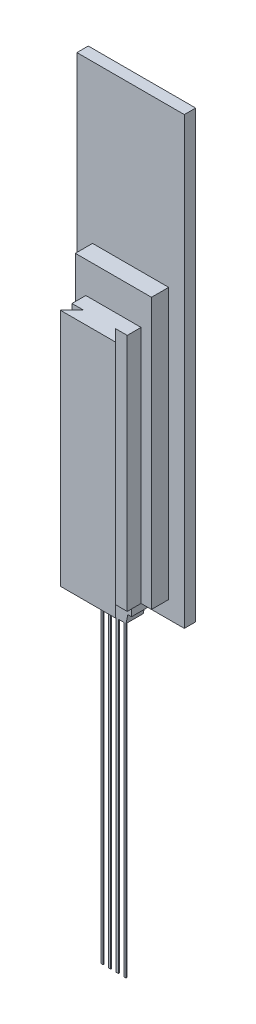
SolidWorks part; units mm, degrees
ref_plane "Front Plane" through (0, 0, 0) normal (0, 0, 1) x (1, 0, 0)
ref_plane "Top Plane" through (0, 0, 0) normal (0, 1, 0) x (1, 0, 0)
ref_plane "Right Plane" through (0, 0, 0) normal (1, 0, 0) x (0, 0, -1)
sketch "Sketch1" plane through (0, 0, 0) normal (0, 0, 1) x (1, 0, 0)
  line L1 (-1.75, 7.25) -> (1.75, 7.25)
  line L2 (-1.75, 7.25) -> (-1.75, -7.25)
  line L3 (-1.75, -7.25) -> (1.75, -7.25)
  line L4 (1.75, 7.25) -> (1.75, -7.25)
  line L5 (-1.75, 7.25) -> (1.75, -7.25) construction
  line L6 (-1.75, -7.25) -> (1.75, 7.25) construction
  point P0 (0, 0)
  dimension "D1" = 3.5
  dimension "D2" = 14.5
extrude "Boss-Extrude1" add sketch "Sketch1" along normal blind 0.37
sketch "Sketch2" plane through (0, 0, 0.37) normal (0, 0, 1) x (1, 0, 0)
  line L0 (-1.75, -7.25) -> (1.75, -7.25) construction
  line L1 (-1.24, 2.12) -> (1.24, 2.12)
  line L2 (-1.24, 2.12) -> (-1.24, -6.69)
  line L3 (-1.24, -6.69) -> (1.24, -6.69)
  line L4 (1.24, 2.12) -> (1.24, -6.69)
  line L5 (-1.24, 2.12) -> (1.24, -6.69) construction
  line L6 (-1.24, -6.69) -> (1.24, 2.12) construction
  line L7 (-0.47, -7.22) -> (-0.41, -7.5037)
  line L8 (0.59, -7.22) -> (-0.59, -7.22)
  line L9 (0.59, -7.22) -> (0.59, -6.69)
  line L10 (0.59, -6.69) -> (-0.59, -6.69)
  line L11 (-0.59, -7.22) -> (-0.59, -6.69)
  line L12 (0.59, -7.22) -> (-0.59, -6.69) construction
  line L13 (0.59, -6.69) -> (-0.59, -7.22) construction
  line L14 (-0.41, -7.5037) -> (0.41, -7.5037)
  line L15 (0.41, -7.5037) -> (0.47, -7.22)
  line L16 (0.47, -7.22) -> (-0.47, -7.22)
  point P0 (0, -2.285)
  point P8 (0, -6.955)
  line M8 (-1.75, -7.25) -> (1.75, -7.25)
  dimension "D1" = 0.56
  dimension "D2" = 2.48
  dimension "D3" = 8.81
  dimension "D4" = 0
  dimension "D5" = 0
  dimension "D6" = 0.53
  dimension "D7" = 1.18
  dimension "D8" = 0.12
  dimension "D9" = 0.12
  dimension "D10" = 0.29
  dimension "D11" = 0.82
  dimension "D12" = 0.29
extrude "Boss-Extrude2" add sketch "Sketch2" along normal blind 0.56 contours L4 L1 L2 L3 | L11 L8 L9 L3 | L14 L15 L7 M8 | L15 L8 L7 M8
sketch "Sketch3" plane through (0, 0, 0.93) normal (0, 0, 1) x (1, 0, 0)
  line L0 (-0.41, -7.5037) -> (-0.34, -7.5037)
  line L1 (-0.41, -7.5037) -> (-0.41, -17.5037)
  line L2 (-0.34, -7.5037) -> (-0.34, -17.5037)
  line L3 (-0.41, -17.5037) -> (-0.34, -17.5037)
  line L4 (-0.41, -7.5037) -> (0.41, -7.5037) construction
  line L5 (-0.16, -7.5037) -> (-0.09, -7.5037)
  line L6 (-0.16, -7.5037) -> (-0.16, -17.5037)
  line L7 (-0.09, -7.5037) -> (-0.09, -17.5037)
  line L8 (-0.16, -17.5037) -> (-0.09, -17.5037)
  line L9 (0.16, -7.5037) -> (0.09, -7.5037)
  line L10 (0.16, -7.5037) -> (0.16, -17.5037)
  line L11 (0.09, -7.5037) -> (0.09, -17.5037)
  line L12 (0.16, -17.5037) -> (0.09, -17.5037)
  line L13 (0.41, -7.5037) -> (0.34, -7.5037)
  line L14 (0.41, -7.5037) -> (0.41, -17.5037)
  line L15 (0.34, -7.5037) -> (0.34, -17.5037)
  line L16 (0.41, -17.5037) -> (0.34, -17.5037)
  dimension "D1" = 0.07
  dimension "D2" = 0.07
  dimension "D3" = 0.07
  dimension "D4" = 0.07
  dimension "D5" = 0
  dimension "D6" = 0
  dimension "D7" = 0
  dimension "D8" = 0.18
  dimension "D9" = 0.18
  dimension "D10" = 10
extrude "Boss-Extrude3" add sketch "Sketch3" against normal blind 0.03
sketch "Sketch5" plane through (0, 0, 0.93) normal (0, 0, 1) x (1, 0, 0)
  line L0 (0.59, -6.69) -> (1.24, -6.69) construction
  line L1 (0.9, -6.69) -> (-0.9, -6.69)
  line L2 (0.9, -6.69) -> (0.9, 1.1)
  line L3 (0.9, 1.1) -> (-0.9, 1.1)
  line L4 (-0.9, -6.69) -> (-0.9, 1.1)
  line L5 (-1.24, 2.12) -> (-1.24, -6.69) construction
  line L6 (1.24, 2.12) -> (1.24, -6.69) construction
  line L7 (-1.24, 2.12) -> (1.24, 2.12) construction
  dimension "D1" = 0.34
  dimension "D2" = 0.34
  dimension "D3" = 1.02
extrude "Boss-Extrude4" add sketch "Sketch5" along normal blind 0.45
sketch "Sketch6" plane through (0, -6.69, 0) normal (0, -1, 0) x (1, 0, 0)
  line L0 (-0.52, 1.38) -> (-0.9, 1.76)
  line L1 (-0.9, 1.38) -> (0.9, 1.38) construction
  line L2 (-0.9, 1.76) -> (0.9, 1.76)
  line L3 (0.9, 1.76) -> (0.52, 1.38)
  line L4 (0.52, 1.38) -> (-0.52, 1.38)
  dimension "D1" = 0.38
  dimension "D2" = 0.38
  dimension "D3" = 45
  dimension "D4" = 0.38
  dimension "D5" = 45
extrude "Boss-Extrude5" add sketch "Sketch6" against normal up to surface (7.79 mm away) up to face at (0, 1.1, 1.155)
sketch "Sketch7" plane through (0, 0, 0.93) normal (0, 0, 1) x (1, 0, 0)
  line L0 (-0.09, -17.5037) -> (-0.09, -7.5037) construction
  line L1 (0.09, -7.5037) -> (0.09, -17.5037) construction
  line L2 (-0.09, -17.5037) -> (0.09, -17.5037)
  line L3 (0.09, -17.5037) -> (0.16, -17.5037) construction
  point P0 (-0.09, -17.5037)
  point P1 (0.09, -17.5037)
  point P3 (-0.09, -15.5037)
  point P5 (0.09, -15.5037)
  point P8 (-0.09, -13.5037)
  point P11 (0.09, -13.5037)
  point P12 (-0.09, -12.5037)
  point P13 (0.09, -12.5037)
  point P14 (-0.09, -11.5037)
  point P15 (0.09, -11.5037)
  point P18 (0.09, -16.5037)
  point P19 (-0.09, -16.5037)
  point P20 (-0.09, -14.5037)
  point P21 (0.09, -14.5037)
  dimension "D1" = 2
  dimension "D2" = 2
  dimension "D3" = 2
  dimension "D4" = 2
  dimension "D5" = 1
  dimension "D6" = 1
  dimension "D7" = 1
  dimension "D8" = 1
  dimension "D9" = 1
  dimension "D10" = 0
  dimension "D11" = 1
  dimension "D12" = 0
